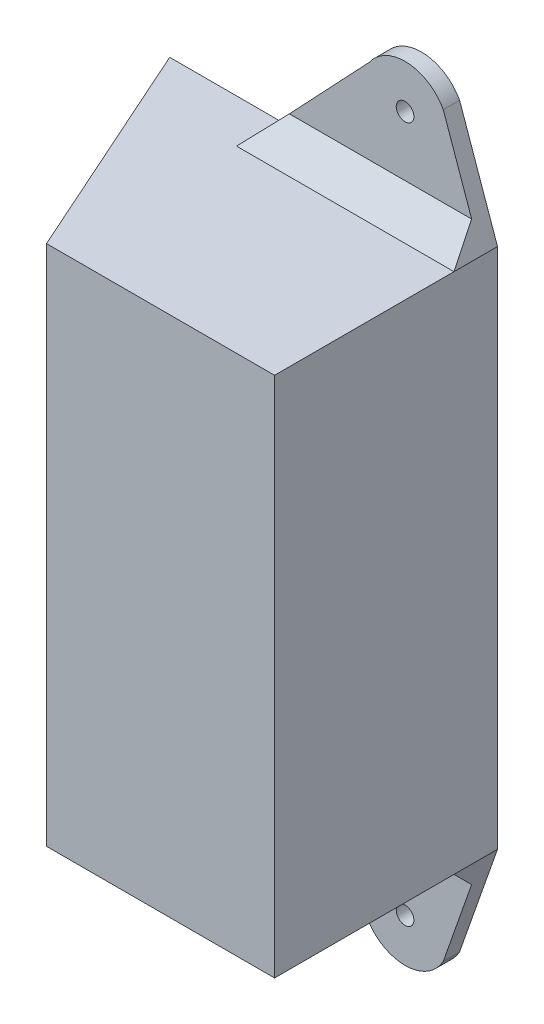
SolidWorks part; units mm, degrees
ref_plane "Alzado" through (0, 0, 0) normal (0, 0, 1) x (1, 0, 0)
ref_plane "Planta" through (0, 0, 0) normal (0, 1, 0) x (1, 0, 0)
ref_plane "Vista lateral" through (0, 0, 0) normal (1, 0, 0) x (0, 0, -1)
sketch "Croquis1" plane through (0, 0, 0) normal (0, 0, 1) x (1, 0, 0)
  line L0 (0, 45) -> (37, 45)
  line L1 (37, 45) -> (37, -45)
  line L2 (37, -45) -> (0, -45)
  line L3 (0, 48) -> (40, 48)
  line L4 (40, 48) -> (40, -48)
  line L5 (40, -48) -> (0, -48)
  line L6 (0, 48) -> (0, 45)
  line L7 (0, -45) -> (0, -48)
  dimension "D1" = 90
  dimension "D2" = 37
  dimension "D4" = 45
  dimension "D3" = 3
extrude "Saliente-Extruir1" add sketch "Croquis1" along normal blind 38
sketch "Croquis2" plane through (0, 0, 0) normal (0, 0, -1) x (-1, 0, 0)
  line L0 (-40, -48) -> (-40, 48) construction
  line L1 (-40, -48) -> (-33.0263, -67.825)
  line L2 (0, -48) -> (-19.442, -68.5818)
  line L3 (-40, -48) -> (0, -48)
  line L4 (0, 0) -> (-65.1391, 0) construction
  line L5 (-40, 48) -> (0, 48)
  line L6 (0, 48) -> (-19.442, 68.5818)
  line L7 (-40, 48) -> (-33.0263, 67.825)
  circle A0 centre (-26, -64) radius 1.625
  arc A1 (-33.0263, -67.825) -> (-19.442, -68.5818) centre (-26, -64) ccw
  arc A2 (-33.0263, 67.825) -> (-19.442, 68.5818) centre (-26, 64) cw
  circle A3 centre (-26, 64) radius 1.625
  dimension "D2" = 3.25
  dimension "D4" = 16
  dimension "D1" = 14
  dimension "D3" = 64
extrude "Saliente-Extruir2" add sketch "Croquis2" against normal blind 3
chamfer "Chaflán1" distance 5 angle 45 2 edges at (20, -48, 3) (20, 48, 3)
sketch "Croquis3" plane through (0, -48, 0) normal (0, -1, 0) x (1, 0, 0)
  line L0 (0, 38) -> (-17, 0)
  line L1 (-17, 0) -> (0, 0)
  line L2 (0, 0) -> (0, 38)
  dimension "D1" = 17
extrude "Saliente-Extruir3" add sketch "Croquis3" against normal blind 3
sketch "Croquis4" plane through (0, 48, 0) normal (0, 1, 0) x (1, 0, 0)
  line L0 (0, 0) -> (0, -38)
  line L1 (0, -38) -> (-17, 0)
  line L2 (-17, 0) -> (0, 0)
  dimension "D1" = 17
extrude "Saliente-Extruir4" add sketch "Croquis4" against normal blind 3
sketch "Croquis6" plane through (0, 0, 38) normal (0, 0, 1) x (1, 0, 0)
  line L1 (40, 48) -> (0, 48)
  line L2 (40, 48) -> (40, -48)
  line L3 (40, -48) -> (0, -48)
  line L4 (0, 48) -> (0, -48)
extrude "Saliente-Extruir5" add sketch "Croquis6" along normal blind 3
sketch "Croquis7" plane through (0, -48, 0) normal (0, -1, 0) x (1, 0, 0)
  line L0 (-17, 0) -> (0, 38)
  line L1 (0, 38) -> (0, 41)
  line L3 (-1.9444, 41) -> (-20.2865, 0)
  line L4 (-20.2865, 0) -> (-17, 0)
  line L6 (0, 41) -> (-1.9444, 41)
  dimension "D1" = 3
extrude "Saliente-Extruir6" add sketch "Croquis7" against normal up to vertex (96 mm away)
sketch "Croquis8" plane through (-16.9035, 0, 7.5621) normal (-0.9128, 0, 0.4084) x (0.4084, 0, 0.9128)
  line L0 (6.7157, 38) -> (6.7157, -25.8685) construction
  line L1 (36.6315, 48) -> (-8.2843, 48) construction
  line L2 (-8.2843, 48) -> (-8.2843, -48) construction
  text T0 "<b>SAMI</b>" font "Comic Sans MS" height 20
  dimension "D1" = 10
  dimension "D2" = 15
extrude "Saliente-Extruir7" add sketch "Croquis8" along normal blind 2
